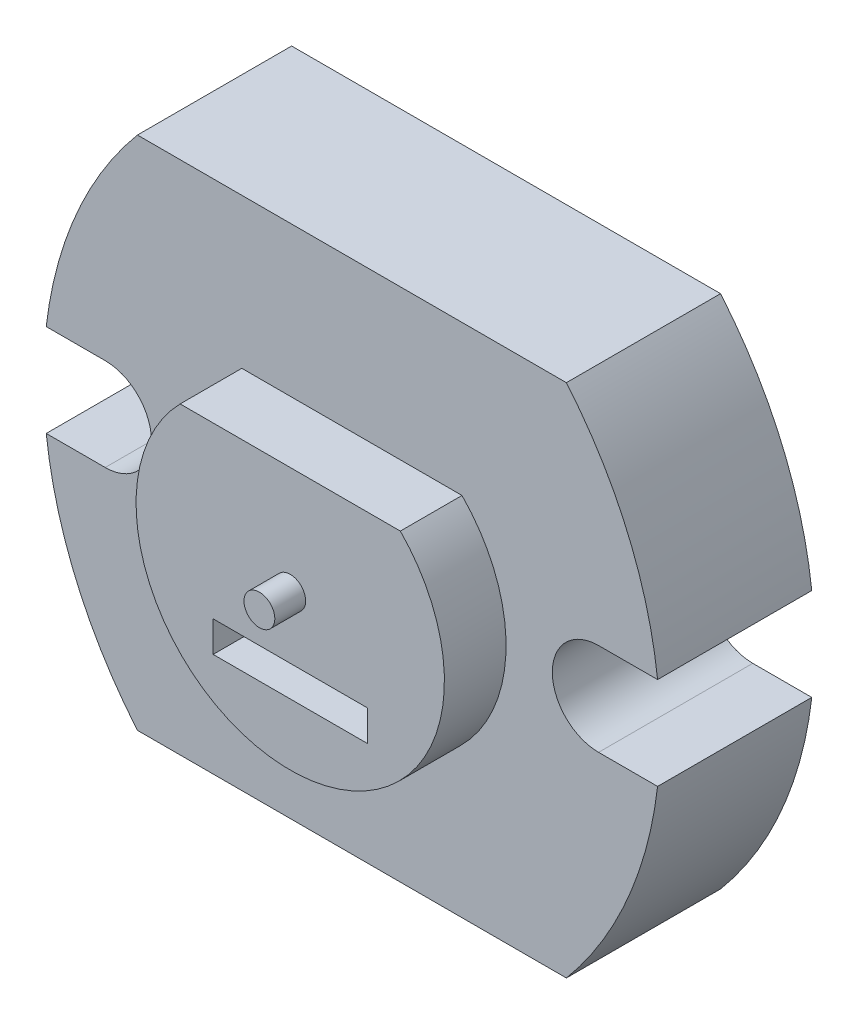
SolidWorks part; units mm, degrees
ref_plane "Front Plane" through (0, 0, 0) normal (0, 0, 1) x (1, 0, 0)
ref_plane "Top Plane" through (0, 0, 0) normal (0, 1, 0) x (1, 0, 0)
ref_plane "Right Plane" through (0, 0, 0) normal (1, 0, 0) x (0, 0, -1)
sketch "Sketch1" plane through (0, 0, 0) normal (0, 0, 1) x (1, 0, 0)
  line L0 (-10, 0) -> (10, 0)
  line L1 (0, 8.36) -> (0, 0) construction
  line L2 (-6.9554, 8.36) -> (6.9554, 8.36)
  line L4 (-6.9554, -8.36) -> (6.9554, -8.36)
  line L6 (-10, 0) -> (10, 0) construction
  arc A0 (-6.9554, -8.36) -> (-6.9554, 8.36) centre (3, 0) cw
  arc A1 (6.9554, -8.36) -> (6.9554, 8.36) centre (-3, 0) ccw
  point P10 (-10, 0)
  dimension "D5" = 13
  dimension "D1" = 8.36
  dimension "D3" = 10
  dimension "D2" = 13.9108
extrude "Boss-Extrude2" add sketch "Sketch1" along normal blind 5 contours L0 A1 L2 A0 | L4 A1 L0 A0
sketch "Sketch2" plane through (0, 0, 5) normal (0, 0, 1) x (1, 0, 0)
  line L0 (0, 8.36) -> (0, -8.36) construction
  line L1 (-6.9554, 8.36) -> (6.9554, 8.36) construction
  line L2 (-6.9554, -8.36) -> (6.9554, -8.36) construction
  line L3 (-10, 0) -> (10, 0) construction
  line L4 (-8, 1.5) -> (-9.9132, 1.5)
  line L5 (-8, -1.5) -> (-9.9132, -1.5)
  line L6 (8, -1.5) -> (9.9132, -1.5)
  line L7 (8, 1.5) -> (9.9132, 1.5)
  line L8 (-9.9132, 1.5) -> (-10.3171, 1.5)
  line L9 (-9.9132, -1.5) -> (-10.3171, -1.5)
  line L10 (9.9132, 1.5) -> (10.3171, 1.5)
  line L11 (9.9132, -1.5) -> (10.3171, -1.5)
  arc A0 (-8, -1.5) -> (-8, 1.5) centre (-8, 0) ccw
  arc A2 (6.9554, -8.36) -> (6.9554, 8.36) centre (-3, 0) ccw construction
  arc A3 (-6.9554, 8.36) -> (-6.9554, -8.36) centre (3, 0) ccw construction
  arc A4 (8, -1.5) -> (8, 1.5) centre (8, 0) cw
  arc A5 (-10.3171, 1.5) -> (-10.3171, -1.5) centre (0, 0) ccw
  arc A6 (10.3171, -1.5) -> (10.3171, 1.5) centre (0, 0) ccw
  dimension "D1" = 3
  dimension "D3" = 20.8512
  dimension "D2" = 2
extrude "Cut-Extrude1" cut sketch "Sketch2" against normal blind 5
sketch "Sketch3" plane through (0, 0, 5) normal (0, 0, 1) x (1, 0, 0)
  circle A0 centre (0, 0) radius 0.5
  dimension "D1" = 1
extrude "Boss-Extrude3" add sketch "Sketch3" along normal blind 3
sketch "Sketch4" plane through (0, 0, 5) normal (0, 0, 1) x (1, 0, 0)
  line L0 (0, -8.36) -> (0, 8.36) construction
  line L1 (-6.9554, -8.36) -> (6.9554, -8.36) construction
  line L2 (-6.9554, 8.36) -> (6.9554, 8.36) construction
  line L3 (-3.5707, 3.5) -> (3.5707, 3.5)
  arc A0 (-3.5707, 3.5) -> (3.5707, 3.5) centre (0, 0) ccw
  dimension "D1" = 10
  dimension "D2" = 3.5
extrude "Boss-Extrude4" add sketch "Sketch4" along normal blind 2
sketch "Sketch5" plane through (0, 0, 7) normal (0, 0, 1) x (1, 0, 0)
  line L0 (0, 3.5) -> (0, -5) construction
  line L2 (3.5707, 3.5) -> (-3.5707, 3.5) construction
  line L4 (-2.5, -2) -> (2.5, -2)
  line L5 (-2.5, -2) -> (-2.5, -3)
  line L6 (-2.5, -3) -> (2.5, -3)
  line L7 (2.5, -2) -> (2.5, -3)
  arc A0 (-3.5707, 3.5) -> (3.5707, 3.5) centre (0, 0) ccw construction
  point P11 (0, -3)
  dimension "D1" = 1
  dimension "D2" = 3
  dimension "3" = 5
extrude "Cut-Extrude2" cut sketch "Sketch5" against normal blind 2
